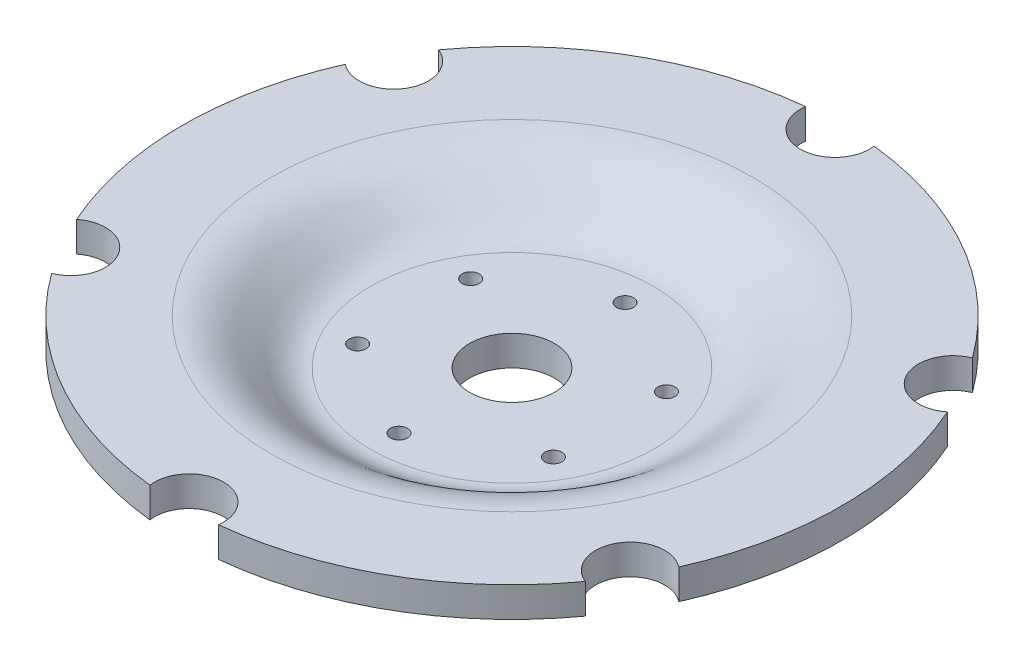
SolidWorks part; units mm, degrees
other "design space"
material "Alloy Steel"
ref_plane "Front" through (0, 0, 0) normal (0, 0, 1) x (1, 0, 0)
ref_plane "Top" through (0, 0, 0) normal (0, 1, 0) x (1, 0, 0)
ref_plane "Right" through (0, 0, 0) normal (1, 0, 0) x (0, 0, -1)
other "Configuration Table"
ref_plane "Plane1" through (0, 0, 0) normal (0, 0, -1) x (-1, 0, 0)
sketch "Sketch1" plane through (0, 0, 0) normal (0, 0, -1) x (-1, 0, 0)
  line L0 (0, -21.28) -> (-47, -21.28)
  line L1 (0, -11.28) -> (0, -21.28)
  line L2 (0, -11.28) -> (-47, -11.28)
  line L3 (-79.9, 3.76) -> (-109.626, 3.76)
  line L4 (-109.626, 3.76) -> (-109.626, -6.24)
  line L5 (-79.9, -6.24) -> (-109.626, -6.24)
  line L6 (0, -15.0433) -> (0, 3.7622) construction
  spline S0 degree 3 poles (-47, -11.28) (-47.3238, -11.28) (-47.9824, -11.2568) (-49.2059, -11.1253) (-50.6525, -10.8135) (-52.3036, -10.2236) (-54.4659, -9.1631) (-57.1691, -7.3507) (-60.5598, -4.6199) (-64.2717, -1.6709) (-67.8472, 0.6398) (-71.126, 2.1511) (-73.8104, 3.0425) (-76.2433, 3.5251) (-78.2919, 3.7255) (-79.368, 3.76) (-79.9, 3.76) knots 0 0 0 0 0.03125 0.0625 0.125 0.1875 0.25 0.375 0.5 0.625 0.75 0.8125 0.875 0.9375 0.96875 1 1 1 1
  spline S1 degree 1 poles (-47, -21.28) (-79.9, -6.24) knots 0 0 1 1 construction
  spline S2 degree 3 poles (-47, -21.28) (-48.1034, -21.28) (-50.3552, -21.1198) (-53.4143, -20.4535) (-56.2438, -19.4392) (-59.6386, -17.7605) (-63.2492, -15.3018) (-66.9207, -12.3328) (-70.2209, -9.727) (-72.7884, -8.0944) (-74.8239, -7.1629) (-76.3668, -6.6519) (-77.7578, -6.3766) (-78.9275, -6.2614) (-79.5814, -6.24) (-79.9, -6.24) knots 0 0 0 0 0.0625 0.125 0.1875 0.25 0.375 0.5 0.625 0.75 0.8125 0.875 0.9375 0.96875 1 1 1 1
  dimension "D1" = 10
revolve "Revolve1" add sketch "Sketch1" angle 360 about L6
hole_wizard "Ø23.0 (23) Diameter Hole2" positions "Sketch5" profile "Sketch4" hole size "Ø23.0" standard "ANSI Metric" end condition through all
sketch "Sketch5" plane through (0, 3.76, 0) normal (0, 1, 0) x (1, 0, 0)
  point P0 (-92.998, 53.6924)
  point P1 (92.998, -53.6924)
  point P2 (92.998, 53.6924)
  point P3 (0, 107.3848)
  point P4 (-92.998, -53.6924)
  point P7 (0, -107.3848)
sketch "Sketch4" plane through (-92.998, 3.76, -53.6924) normal (1, 0, 0) x (0, 0, 1)
  line L0 (0, 0) -> (0, 25.04)
  line L1 (0, 25.04) -> (11.5, 25.04)
  line L2 (11.5, 25.04) -> (11.5, 0)
  line L5 (11.5, 0) -> (0, 0)
  line L11 (0, -6.35) -> (0, 107.95) construction
  dimension "Thru Hole Dia." = 23
  dimension "Thru Hole Depth" = 25.04
hole_wizard "M5 Clearance Hole1" positions "Sketch7" profile "Sketch6" hole size "M5" standard "ANSI Metric"
sketch "Sketch7" plane through (0, -11.28, 0) normal (0, 1, 0) x (1, 0, 0)
  point P0 (-32.5626, 18.8)
  point P1 (0, 37.6)
  point P2 (32.5626, 18.8)
  point P3 (32.5626, -18.8)
  point P4 (0, -37.6)
  point P5 (-32.5626, -18.8)
sketch "Sketch6" plane through (-32.5626, -11.28, -18.8) normal (1, 0, 0) x (0, 0, 1)
  line L0 (0, 0) -> (0, 10)
  line L1 (0, 10) -> (2.82, 10)
  line L2 (2.82, 10) -> (2.82, 0)
  line L5 (2.82, 0) -> (0, 0)
  line L11 (0, -6.35) -> (0, 107.95) construction
  dimension "Thru Hole Dia." = 5.64
  dimension "Thru Hole Depth" = 10
hole_wizard "M25 Clearance Hole1" positions "Sketch9" profile "Sketch8" hole size "M25" standard "ANSI Metric" end condition through all
sketch "Sketch9" plane through (0, -11.28, 0) normal (0, 1, 0) x (1, 0, 0)
  point P0 (0, 0)
sketch "Sketch8" plane through (0, -11.28, 0) normal (1, 0, 0) x (0, 0, 1)
  line L0 (0, 0) -> (0, 10)
  line L1 (0, 10) -> (14.1, 10)
  line L2 (14.1, 10) -> (14.1, 0)
  line L5 (14.1, 0) -> (0, 0)
  line L11 (0, -6.35) -> (0, 107.95) construction
  dimension "Thru Hole Dia." = 28.2
  dimension "Thru Hole Depth" = 10
